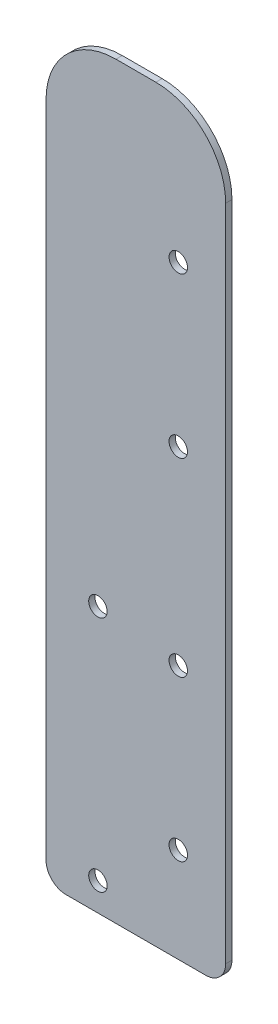
SolidWorks part; units mm, degrees
ref_plane "Front Plane" through (0, 0, 0) normal (0, 0, 1) x (1, 0, 0)
ref_plane "Top Plane" through (0, 0, 0) normal (0, 1, 0) x (1, 0, 0)
ref_plane "Right Plane" through (0, 0, 0) normal (1, 0, 0) x (0, 0, -1)
sketch "Sketch1" plane through (0, 0, 0) normal (0, 0, 1) x (1, 0, 0)
  line L1 (0, -146.6506) -> (0, 146.6506) construction
  line L3 (45.72, 5.08) -> (45.72, 172.72)
  line L5 (40.64, 0) -> (33.655, 0)
  line L7 (66.681, 0) -> (66.681, 88.9) construction
  line L8 (33.655, 0) -> (45.72, 0) construction
  line L9 (33.655, 177.8) -> (33.655, 0) construction
  line L10 (118.1346, 0) -> (-118.1346, 0) construction
  line L11 (66.681, 88.9) -> (0, 88.9) construction
  line L18 (66.681, 88.9) -> (66.681, 177.8) construction
  line L19 (66.681, 177.8) -> (0, 177.8) construction
  line L20 (0, 4.7616) -> (0, 172.72)
  line L23 (5.07, 0) -> (33.655, 0)
  line L27 (19.7982, 0.039) -> (19.7982, 177.8) construction
  line L28 (33.655, 24.13) -> (0, 24.13) construction
  line L36 (66.681, 0) -> (0, 0) construction
  line L46 (17.78, 190.5) -> (27.94, 190.5)
  line L47 (19.9023, 177.8) -> (19.9023, 190.5) construction
  line L49 (19.9023, 190.5) -> (-14.4304, 190.5) construction
  line L50 (20.4442, 160.274) -> (0, 160.274) construction
  line L51 (45.72, 10.2129) -> (43.18, 10.2129) construction
  line L52 (43.18, 10.2129) -> (43.18, 0.6806) construction
  line L53 (43.18, 0.6806) -> (43.18, 181.8781) construction
  line L54 (13.208, 0.039) -> (13.208, 189.9021) construction
  circle A0 centre (33.655, 24.13) radius 2.3495
  circle A1 centre (33.655, 64.77) radius 2.3495
  arc A5 (40.64, 0) -> (45.72, 5.08) centre (40.64, 5.08) ccw
  arc A6 (5.07, 0) -> (0, 4.7616) centre (5.07, 5.08) cw
  circle A7 centre (33.655, 113.03) radius 2.3495
  circle A8 centre (33.655, 153.67) radius 2.3495
  arc A13 (45.72, 172.72) -> (27.94, 190.5) centre (27.94, 172.72) ccw
  arc A14 (0, 172.72) -> (17.78, 190.5) centre (17.78, 172.72) cw
  circle A15 centre (13.208, 7.151) radius 2.3495
  circle A17 centre (13.208, 67.6031) radius 2.3495
  point P24 (0, 190.5)
  point P30 (0, 0)
  point P38 (0, 190.5)
  point P39 (19.7982, 0.039)
  point P42 (0, 185.42)
  point P46 (40.64, 185.0608)
  point P49 (5.07, 0)
  point P52 (0, 190.5)
  dimension "D7" = 4.699
  dimension "D5" = 24.13
  dimension "D6" = 4.699
  dimension "D9" = 24.13
  dimension "D11" = 88.9
  dimension "D12" = 5.08
  dimension "D13" = 4.699
  dimension "D15" = 4.699
  dimension "D17" = 4.699
  dimension "D19" = 17.78
  dimension "D22" = 20.32
  dimension "D26" = 2.54
  dimension "D20" = 32.512
  dimension "D25" = 12.7
  dimension "D27" = 9.525
  dimension "D29" = 4.699
  dimension "D23" = 28.585
  dimension "D14" = 67.6031
  dimension "D1" = 190.5
  dimension "D2" = 45.72
  dimension "D3" = 88.9
  dimension "D4" = 9.525
  dimension "D8" = 40.64
  dimension "D10" = 24.13
  dimension "D16" = 40.64
  dimension "D18" = 24.13
  dimension "D21" = 30.226
  dimension "D28" = 64.77
  dimension "D30" = 7.151
extrude "Boss-Extrude2" add sketch "Sketch1" along normal blind 1.6002
